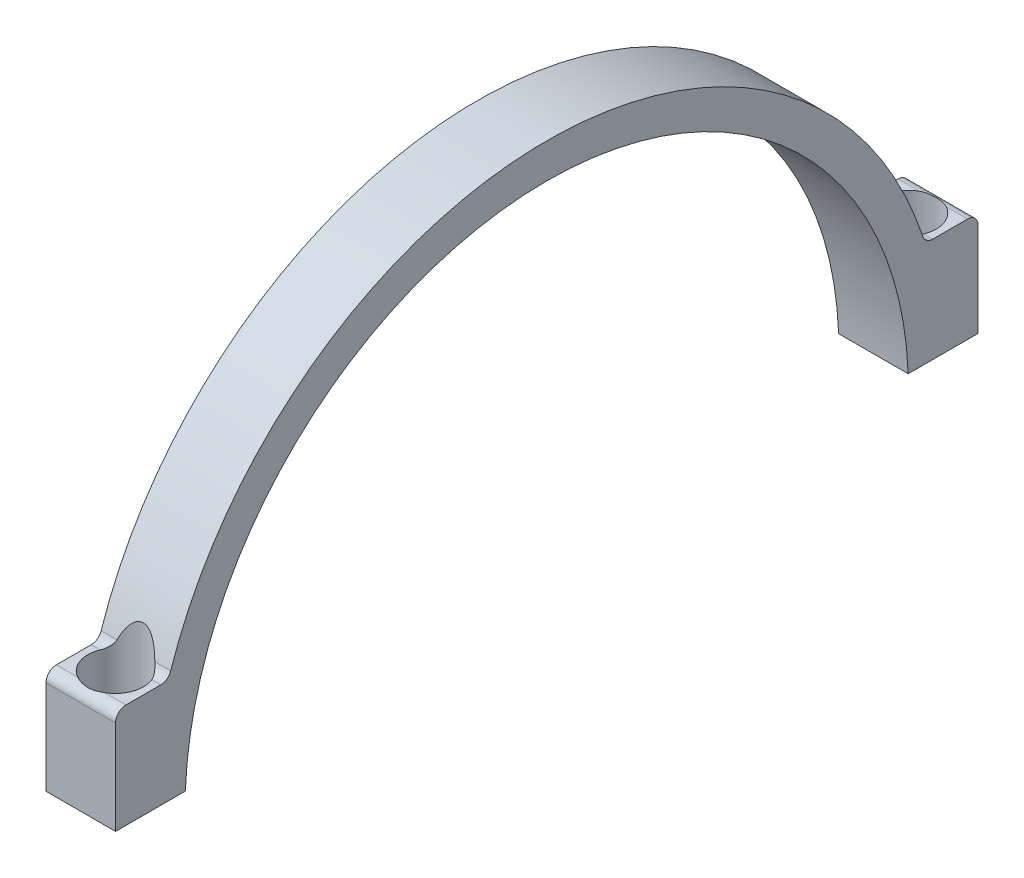
SolidWorks part; units mm, degrees
material "High Density Carbon Steel"
ref_plane "Front Plane" through (0, 0, 0) normal (0, 0, 1) x (1, 0, 0)
ref_plane "Top Plane" through (0, 0, 0) normal (0, 1, 0) x (1, 0, 0)
ref_plane "Right Plane" through (0, 0, 0) normal (1, 0, 0) x (0, 0, -1)
sketch "Sketch1" plane through (0, 0, 0) normal (1, 0, 0) x (0, 0, -1)
  line L2 (-62, 2) -> (-51.9615, 2)
  line L3 (51.9615, 2) -> (62, 2)
  line L4 (-62, 2) -> (-62, 15.5)
  line L5 (-60.5, 17) -> (-55.4977, 17)
  line L6 (62, 2) -> (62, 15.5)
  line L7 (60.5, 17) -> (55.4977, 17)
  arc A0 (51.9615, 2) -> (-51.9615, 2) centre (0, 0) ccw
  arc A1 (54.0747, 18.0256) -> (-54.0747, 18.0256) centre (0, 0) ccw
  circle A2 centre (0, 0) radius 57 construction
  circle A3 centre (0, 0) radius 52 construction
  arc A4 (-62, 15.5) -> (-60.5, 17) centre (-60.5, 15.5) cw
  arc A5 (-55.4977, 17) -> (-54.0747, 18.0256) centre (-55.4977, 18.5) ccw
  arc A6 (55.4977, 17) -> (54.0747, 18.0256) centre (55.4977, 18.5) cw
  arc A7 (62, 15.5) -> (60.5, 17) centre (60.5, 15.5) ccw
  dimension "D1" = 104
  dimension "D2" = 1.5
  dimension "D5" = 5
extrude "Boss-Extrude1" add sketch "Sketch1" along normal blind 10
hole_wizard "CBORE for M4 Cheese Head Screw1" positions "Sketch5" profile "Sketch4" counterbore size "M4" standard "ISO"
sketch "Sketch5" plane through (0, 17, 0) normal (0, 1, 0) x (1, 0, 0)
  line L0 (10, 60.5) -> (10, 55.4977) construction
  line L1 (10, -62) -> (0, -62) construction
  line L2 (10, 62) -> (0, 62) construction
  line L4 (10, -55.4977) -> (10, -60.5) construction
  point P0 (5, 57)
  point P11 (5, -57)
  dimension "D1" = 5
  dimension "D2" = 5
  dimension "D3" = 5
  dimension "D4" = 5
sketch "Sketch4" plane through (5, 17, -57) normal (1, 0, 0) x (0, 0, 1)
  line L0 (0, 0) -> (0, 21.2919)
  line L1 (0, 21.2919) -> (2.15, 20)
  line L2 (2.15, 20) -> (2.15, 6.6)
  line L3 (2.15, 6.6) -> (4, 6.6)
  line L4 (4, 6.6) -> (4, 0)
  line L5 (4, 0) -> (0, 0)
  line L10 (0, 21.2919) -> (-2.15, 20) construction
  line L11 (0, -6.35) -> (0, 107.95) construction
  dimension "Hole Dia." = 4.3
  dimension "Hole Depth" = 20
  dimension "C'Bore Dia." = 8
  dimension "C'Bore Depth" = 6.6
  dimension "Drill Angle" = 118
sketch "Sketch6" plane through (0, 17, 0) normal (0, 1, 0) x (1, 0, 0)
  circle A0 centre (5, 57) radius 4
  circle A1 centre (5, -57) radius 4
extrude "Cut-Extrude1" cut sketch "Sketch6" along normal blind 8
